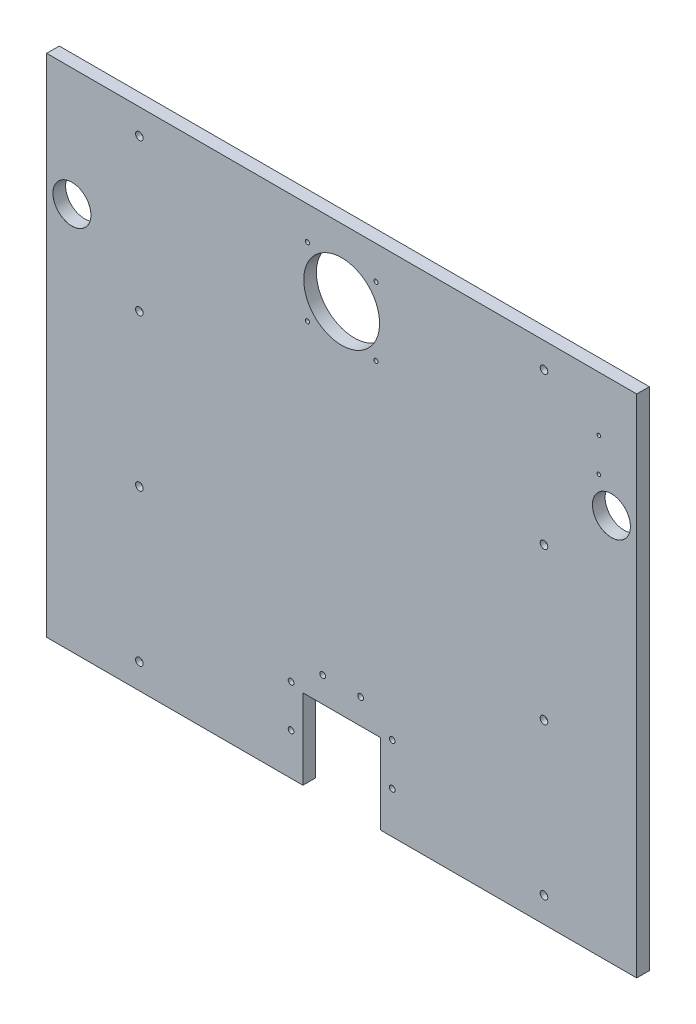
SolidWorks part; units mm, degrees
ref_plane "前视基准面" through (0, 0, 0) normal (0, 0, 1) x (1, 0, 0)
ref_plane "上视基准面" through (0, 0, 0) normal (0, 1, 0) x (1, 0, 0)
ref_plane "右视基准面" through (0, 0, 0) normal (1, 0, 0) x (0, 0, -1)
ref_plane "基准面1" through (0, 0, -190) normal (0, 0, -1) x (-1, 0, 0)
sketch "草图1" plane through (0, 0, -190) normal (0, 0, -1) x (-1, 0, 0)
  line L0 (-350, 1820) -> (-350, 1220)
  line L1 (-350, 1220) -> (350, 1220)
  line L2 (350, 1220) -> (350, 1820)
  line L3 (350, 1820) -> (-350, 1820)
extrude "凸台-拉伸1" add sketch "草图1" against normal blind 15
sketch "草图2" plane through (0, 0, -175) normal (0, 0, 1) x (1, 0, 0)
  line L0 (-46, 1220) -> (46, 1220)
  line L1 (46, 1220) -> (46, 1315)
  line L2 (46, 1315) -> (-46, 1315)
  line L3 (-46, 1315) -> (-46, 1220)
extrude "切除-拉伸1" cut sketch "草图2" against normal through all
hole_wizard "Ø5.0 (5) 直径孔1" positions "草图4" profile "草图3" hole size "Ø5.0" standard "ANSI Metric" end condition through all
sketch "草图4" plane through (0, 0, -175) normal (0, 0, 1) x (1, 0, 0)
  point P0 (-40.6586, 1699.3414)
  point P1 (40.6586, 1699.3414)
  point P2 (40.6586, 1780.6586)
  point P3 (-40.6586, 1780.6586)
sketch "草图3" plane through (-40.6586, 1699.3414, -175) normal (1, 0, 0) x (0, -1, 0)
  line L0 (0, 0) -> (0, 15)
  line L1 (0, 15) -> (2.5, 15)
  line L2 (2.5, 15) -> (2.5, 0)
  line L5 (2.5, 0) -> (0, 0)
  line L11 (0, -6.35) -> (0, 107.95) construction
  dimension "通孔孔直径" = 5
  dimension "通孔孔深度" = 15
hole_wizard "Ø6.8 (6.8) 直径孔1" positions "草图6" profile "草图5" hole size "Ø6.8" standard "ANSI Metric"
sketch "草图6" plane through (0, 0, -175) normal (0, 0, 1) x (1, 0, 0)
  point P0 (60, 1319.4722)
  point P1 (60, 1269.4722)
  point P2 (-60, 1269.4722)
  point P3 (-60, 1319.4722)
  point P4 (22.5, 1345)
  point P5 (-22.5, 1345)
sketch "草图5" plane through (60, 1319.4722, -175) normal (1, 0, 0) x (0, -1, 0)
  line L0 (0, 0) -> (0, 15)
  line L1 (0, 15) -> (3.4, 15)
  line L2 (3.4, 15) -> (3.4, 0)
  line L5 (3.4, 0) -> (0, 0)
  line L11 (0, -6.35) -> (0, 107.95) construction
  dimension "通孔孔直径" = 6.8
  dimension "通孔孔深度" = 15
hole_wizard "M8 六角头螺栓的柱形沉头孔1" positions "草图8" profile "草图7" counterbore size "M8" standard "ANSI Metric"
sketch "草图8" plane through (0, 0, -190) normal (0, 0, -1) x (-1, 0, 0)
  point P0 (240, 1250)
  point P1 (240, 1430)
  point P2 (240, 1610)
  point P3 (240, 1790)
  point P4 (-240, 1250)
  point P5 (-240, 1430)
  point P6 (-240, 1610)
  point P7 (-240, 1790)
sketch "草图7" plane through (-240, 1250, -190) normal (1, 0, 0) x (0, 1, 0)
  line L0 (0, 0) -> (0, 15)
  line L1 (0, 15) -> (4.5, 15)
  line L3 (4.5, 15) -> (4.5, 9)
  line L4 (4.5, 9) -> (7.5, 9)
  line L5 (7.5, 9) -> (7.5, 0)
  line L7 (7.5, 0) -> (0, 0)
  line L11 (0, -6.35) -> (0, 107.95) construction
  dimension "通孔孔直径" = 9
  dimension "通孔孔深度" = 15
  dimension "柱形沉头孔直径" = 15
  dimension "柱形沉头孔深度" = 9
hole_wizard "Ø4.2 (4.2) 直径孔1" positions "草图10" profile "草图9" hole size "Ø4.2" standard "ANSI Metric"
sketch "草图10" plane through (0, 0, -175) normal (0, 0, 1) x (1, 0, 0)
  point P0 (305, 1715)
  point P1 (305, 1755)
sketch "草图9" plane through (305, 1715, -175) normal (1, 0, 0) x (0, -1, 0)
  line L0 (0, 0) -> (0, 13.6618)
  line L1 (0, 13.6618) -> (2.1, 12.4)
  line L2 (2.1, 12.4) -> (2.1, 0)
  line L5 (2.1, 0) -> (0, 0)
  line L10 (0, 13.6618) -> (-2.1, 12.4) construction
  line L11 (0, -6.35) -> (0, 107.95) construction
  dimension "孔直径" = 4.2
  dimension "孔深度" = 12.4
  dimension "导头角度" = 118
hole_wizard "M80 间隙孔1" positions "草图12" profile "草图11" hole size "M80" standard "ANSI Metric"
sketch "草图12" plane through (0, 0, -190) normal (0, 0, -1) x (-1, 0, 0)
  point P0 (0, 1740)
sketch "草图11" plane through (0, 1740, -190) normal (1, 0, 0) x (0, 1, 0)
  line L0 (0, 0) -> (0, 15)
  line L1 (0, 15) -> (45, 15)
  line L2 (45, 15) -> (45, 0)
  line L5 (45, 0) -> (0, 0)
  line L11 (0, -6.35) -> (0, 107.95) construction
  dimension "通孔孔直径" = 90
  dimension "通孔孔深度" = 15
hole_wizard "M39 间隙孔1" positions "草图14" profile "草图13" hole size "M39" standard "ANSI Metric" end condition through all
sketch "草图14" plane through (0, 0, -175) normal (0, 0, 1) x (1, 0, 0)
  point P0 (-320, 1680)
  point P1 (320, 1680)
sketch "草图13" plane through (-320, 1680, -175) normal (1, 0, 0) x (0, -1, 0)
  line L0 (0, 0) -> (0, 15)
  line L1 (0, 15) -> (22.5, 15)
  line L2 (22.5, 15) -> (22.5, 0)
  line L5 (22.5, 0) -> (0, 0)
  line L11 (0, -6.35) -> (0, 107.95) construction
  dimension "通孔孔直径" = 45
  dimension "通孔孔深度" = 15
chamfer "倒角1" distance 0.025 angle 45 2 edges at (342.5, 1680, -175) (-297.5, 1680, -175)
